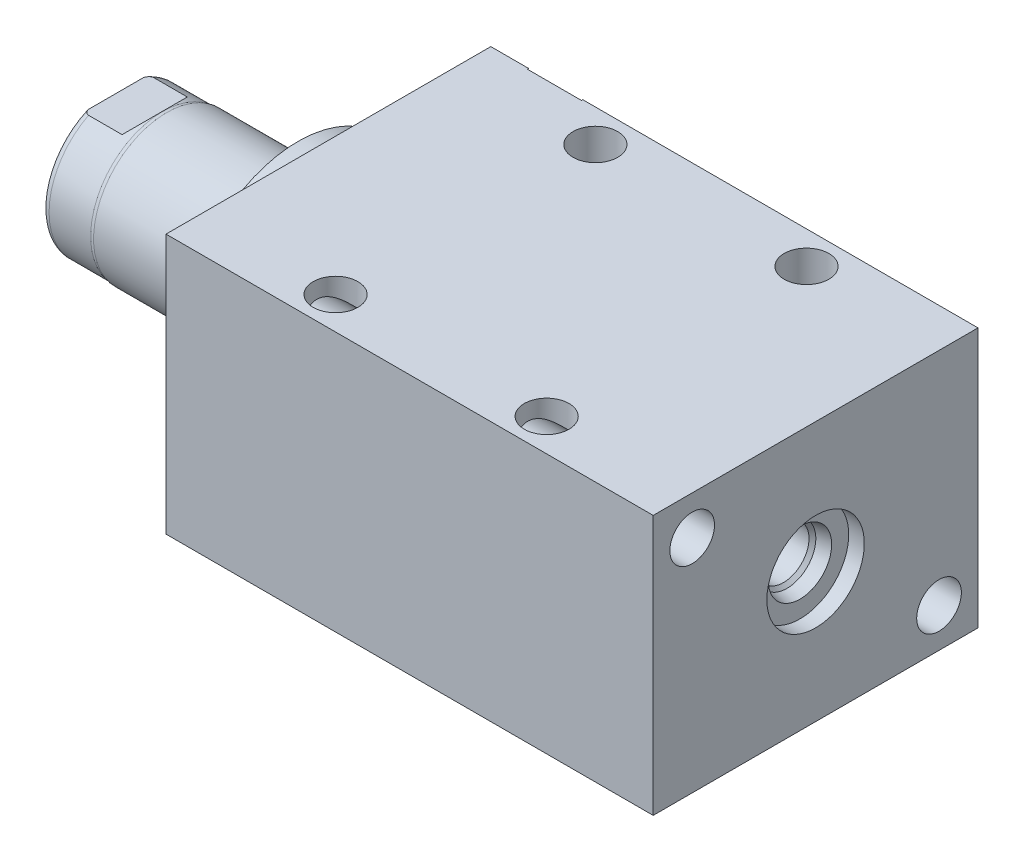
SolidWorks part; units mm, degrees
material "Alloy Steel"
ref_plane "Front Plane" through (0, 0, 0) normal (0, 0, 1) x (1, 0, 0)
ref_plane "Top Plane" through (0, 0, 0) normal (0, 1, 0) x (1, 0, 0)
ref_plane "Right Plane" through (0, 0, 0) normal (1, 0, 0) x (0, 0, -1)
ref_plane "Plane1" through (0, 0, 0) normal (1, 0, 0) x (0, 0, -1)
sketch "Sketch1" plane through (0, 0, 0) normal (1, 0, 0) x (0, 0, -1)
  line L0 (-31.75, 25.4) -> (31.75, 25.4)
  line L1 (31.75, 25.4) -> (31.75, -25.4)
  line L2 (31.75, -25.4) -> (-31.75, -25.4)
  line L3 (-31.75, -25.4) -> (-31.75, 25.4)
  line L4 (0, -24.4475) -> (0, 24.4475) construction
  dimension "D1" = 50.8
  dimension "D2" = 25.4
  dimension "D3" = 63.5
extrude "Extrude1" add sketch "Sketch1" along normal blind 95.25
ref_plane "Plane12" through (0, 17.4752, 0) normal (0, 1, 0) x (-1, 0, 0)
sketch "S2D0002" plane through (0, 17.4752, 0) normal (0, 1, 0) x (-1, 0, 0)
  line L0 (-18.8849, -31.496) -> (-22.225, -31.496)
  line L1 (-18.8849, -31.496) -> (-18.3423, -28.9433)
  line L2 (-18.3423, -28.9433) -> (-17.6784, -28.2794)
  line L3 (-17.6784, -28.2794) -> (-17.6784, -17.526)
  line L4 (-17.6784, -17.526) -> (-12.7, -17.526)
  line L5 (-12.7, -17.526) -> (-12.7, -31.75)
  line L6 (-12.7, -19.1384) -> (-12.7, 0.6985) construction
  line L7 (0, -31.75) -> (0, 31.75) construction
  line L8 (-22.225, -31.75) -> (-22.225, -31.496)
  line L9 (-95.25, -31.75) -> (0, -31.75) construction
  line L10 (-22.225, -31.75) -> (-12.7, -31.75)
  dimension "D1" = 14.224
  dimension "D2" = 12.7
  dimension "D3" = 9.9568
  dimension "D4" = 45
  dimension "D5" = 12.3698
  dimension "D6" = 12
  dimension "D7" = 2.5527
  dimension "D8" = 0.254
  dimension "D9" = 19.05
revolve "Cut-Revolve1" cut sketch "S2D0002" angle 360 about L6
ref_plane "Plane3" through (41.148, 0, -25.146) normal (0, 1, 0) x (1, 0, 0)
sketch "Sketch3" plane through (41.148, 0, -25.146) normal (0, 1, 0) x (1, 0, 0)
  line L0 (45.1993, 6.35) -> (48.5394, 6.35)
  line L1 (45.1993, 6.35) -> (44.6567, 3.7973)
  line L2 (44.6567, 3.7973) -> (43.9928, 3.1334)
  line L3 (43.9928, 3.1334) -> (43.9928, -7.62)
  line L4 (43.9928, -7.62) -> (39.0144, -7.62)
  line L5 (39.0144, -7.62) -> (39.0144, 6.604)
  line L6 (39.0144, -21.9564) -> (39.0144, 0.6985) construction
  line L7 (-41.148, 6.604) -> (-41.148, -56.896) construction
  line L8 (48.5394, 6.604) -> (48.5394, 6.35)
  line L9 (54.102, 6.604) -> (-23.1638, 6.604) construction
  line L10 (48.5394, 6.604) -> (39.0144, 6.604)
  dimension "D1" = 14.224
  dimension "D2" = 80.1624
  dimension "D3" = 9.9568
  dimension "D4" = 45
  dimension "D5" = 12
  dimension "D6" = 12.3698
  dimension "D7" = 2.5527
  dimension "D8" = 0.254
  dimension "D9" = 19.05
revolve "Cut-Revolve2" cut sketch "Sketch3" angle 360 about L6
ref_plane "Plane4" through (53.975, 0, 0) normal (0, 0, 1) x (0, -1, 0)
sketch "Sketch4" plane through (53.975, 0, 0) normal (0, 0, 1) x (0, -1, 0)
  line L0 (6.1849, 38.227) -> (9.525, 38.227)
  line L1 (6.1849, 38.227) -> (5.6423, 35.6743)
  line L2 (5.6423, 35.6743) -> (4.9784, 35.0104)
  line L3 (4.9784, 35.0104) -> (4.9784, 26.8732)
  line L4 (4.9784, 26.8732) -> (0, 26.8732)
  line L5 (0, 26.8732) -> (0, 41.275)
  line L6 (0, -15.0954) -> (0, 0.5677) construction
  line L7 (0, 41.275) -> (9.525, 41.275)
  line L9 (-25.4, 41.275) -> (25.4, 41.275) construction
  line L10 (9.525, 41.275) -> (9.525, 38.227)
  dimension "D1" = 11.3538
  dimension "D2" = 9.9568
  dimension "D3" = 3.048
  dimension "D4" = 19.05
  dimension "D5" = 2.5527
  dimension "D6" = 12
  dimension "D7" = 45
  dimension "D8" = 12.3698
revolve "Cut-Revolve3" cut sketch "Sketch4" angle 360 about L6
sketch "Sketch5" plane through (0, 0, 0) normal (-1, 0, 0) x (0, 0, 1)
  circle A0 centre (0, 0) radius 22.225
  dimension "D1" = 44.45
extrude "Extrude2" add sketch "Sketch5" along normal blind 5.969
ref_plane "Plane5" through (0, 0, 0) normal (0, -1, 0) x (0, 0, 1)
sketch "Sketch6" plane through (0, 0, 0) normal (0, -1, 0) x (0, 0, 1)
  line L0 (0, 5.969) -> (-14.2875, 5.969)
  line L1 (-14.2875, 5.969) -> (-14.2875, 41.529)
  line L2 (-14.2875, 41.529) -> (0, 41.529)
  line L3 (0, 41.529) -> (0, 5.969)
  line L4 (0, -5.7546) -> (0, 21.1709) construction
  line L5 (22.225, 5.969) -> (-22.225, 5.969) construction
  line L6 (31.75, -95.25) -> (-31.75, -95.25) construction
  dimension "D1" = 136.779
  dimension "D2" = 28.575
revolve "Revolve1" add sketch "Sketch6" angle 360 about L4
ref_plane "Plane6" through (-18.5113, 3.2639, 0) normal (0, 0, 1) x (0, 1, 0)
sketch "S2D0001" plane through (-18.5113, 3.2639, 0) normal (0, 0, 1) x (0, 1, 0)
  line L0 (2.286, 20.95) -> (2.286, 6.6347)
  line L1 (2.286, 6.6347) -> (-3.2639, 6.6347)
  line L2 (3.4798, 23.0177) -> (-3.2639, 23.0177)
  line L3 (-3.2639, 23.0177) -> (-3.2639, 6.6347)
  line L4 (2.286, 20.95) -> (3.4798, 23.0177)
  line L5 (-3.2639, -18.5113) -> (-3.2639, 2.765) construction
  line L6 (11.0236, 23.0177) -> (-17.5514, 23.0177) construction
  dimension "D1" = 30
  dimension "D2" = 13.4874
  dimension "D3" = 11.0998
  dimension "D4" = 16.383
revolve "Cut-Revolve4" cut sketch "S2D0001" angle 360 about L5
ref_plane "Plane7" through (0, 0, 0) normal (0, 1, 0) x (0, 0, -1)
sketch "Sketch8" plane through (0, 0, 0) normal (0, 1, 0) x (0, 0, -1)
  line L0 (-14.2875, 31.623) -> (-14.097, 32.385)
  line L1 (-14.097, 32.385) -> (-14.097, 40.513)
  line L2 (0, 12.6594) -> (0, 20.8178) construction
  line L3 (-14.2875, 31.623) -> (-14.2875, 41.529)
  line L4 (-13.7089, 41.529) -> (-14.2875, 41.529)
  line L5 (14.2875, 41.529) -> (-14.2875, 41.529) construction
  line L6 (-14.2875, 41.529) -> (-14.2875, 5.969) construction
  arc A0 (-13.7089, 41.529) -> (-14.097, 40.513) centre (-12.573, 40.513) ccw
  dimension "D2" = 1.524
  dimension "D1" = 28.194
  dimension "D3" = 1.016
  dimension "D4" = 0.762
  dimension "D5" = 9.144
revolve "Cut-Revolve5" cut sketch "Sketch8" angle 360 about L2
ref_plane "Plane11" through (0, 0, 0) normal (0, 0, -1) x (0, -1, 0)
sketch "Sketch12" plane through (0, 0, 0) normal (0, 0, -1) x (0, -1, 0)
  line L0 (12.573, 41.529) -> (12.573, 33.9598)
  line L1 (12.573, 33.9598) -> (14.097, 32.4358)
  line L2 (-12.573, 41.529) -> (-12.573, 33.9598)
  line L3 (-12.573, 33.9598) -> (-14.097, 32.4358)
  line L4 (12.573, 41.529) -> (14.097, 41.529)
  line L5 (0, 13.7262) -> (0, 20.767) construction
  line L6 (-14.097, 32.4358) -> (-14.097, 41.529)
  line L7 (13.7089, 41.529) -> (-13.7089, 41.529) construction
  line L8 (14.097, 32.385) -> (14.097, 40.513) construction
  line L9 (14.097, 32.4358) -> (14.097, 41.529)
  line L10 (-12.573, 41.529) -> (-14.097, 41.529)
  dimension "D1" = 25.146
  dimension "D2" = 7.5692
  dimension "D3" = 45
extrude "Cut-Extrude4" cut sketch "Sketch12" against normal mid plane 60.96
hole_wizard "Hole1" positions "Sketch15" profile "Sketch14" legacy end condition up to next
sketch "Sketch15" plane through (0, 0, 0) normal (-1, 0, 0) x (0, 0, 1)
  line L0 (0, 0) -> (-29.9914, 0) construction
  line L1 (0, 0) -> (0, 25.7648) construction
  point P0 (-24.13, -17.78)
  point P11 (24.13, 17.78)
  dimension "D1" = 17.78
  dimension "D2" = 24.13
  dimension "D3" = 35.56
  dimension "D4" = 48.26
sketch "Sketch14" plane through (0, -17.78, -24.13) normal (0, 1, 0) x (0, 0, 1)
  line L0 (0, 0) -> (0, 95.25)
  line L1 (0, 95.25) -> (4.3688, 95.25)
  line L2 (4.3688, 95.25) -> (4.3688, 0)
  line L3 (4.3688, 0) -> (0, 0)
  line L4 (0, 110) -> (0, -10) construction
  dimension "Diameter" = 8.7376
  dimension "Depth" = 95.25
hole_wizard "Hole2" positions "Sketch17" profile "Sketch16" legacy
sketch "Sketch17" plane through (0, 25.4, 0) normal (0, 1, 0) x (-1, 0, 0)
  line L0 (0, 0) -> (-59.3363, 0) construction
  line L1 (0, -31.75) -> (0, 31.75) construction
  point P0 (-26.797, -25.4)
  point P9 (-26.797, 25.4)
  dimension "D1" = 50.8
  dimension "D2" = 26.797
sketch "Sketch16" plane through (26.797, 25.4, -25.4) normal (1, 0, 0) x (0, 0, 1)
  line L0 (0, 0) -> (0, 50.8)
  line L1 (0, 50.8) -> (4.3688, 50.8)
  line L2 (4.3688, 50.8) -> (4.3688, 0)
  line L3 (4.3688, 0) -> (0, 0)
  line L4 (0, 110) -> (0, -10) construction
  dimension "Diameter" = 8.7376
  dimension "Depth" = 50.8
pattern_linear "LPattern1" count 2 spacing 41.275 along (1, 0, 0) of "Hole2"
